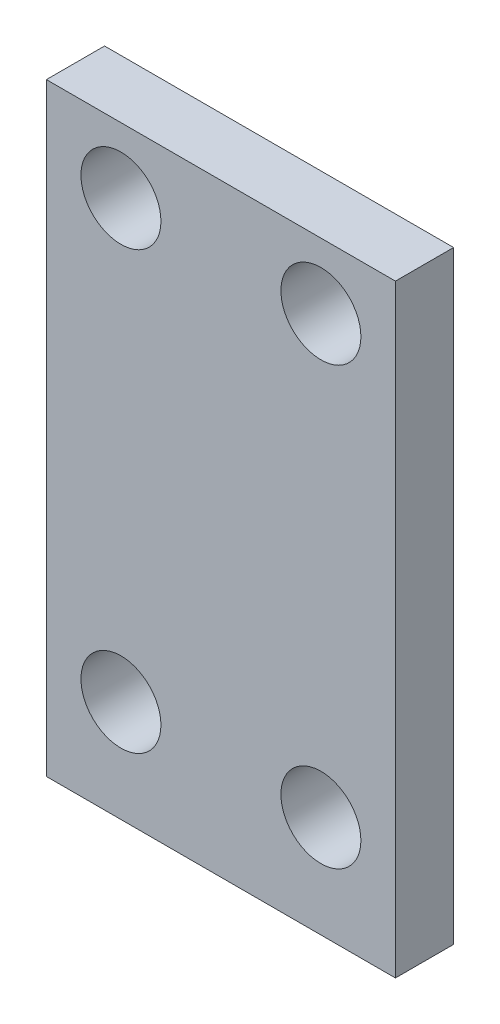
SolidWorks part; units mm, degrees
ref_plane "前视基准面" through (0, 0, 0) normal (0, 0, 1) x (1, 0, 0)
ref_plane "上视基准面" through (0, 0, 0) normal (0, 1, 0) x (1, 0, 0)
ref_plane "右视基准面" through (0, 0, 0) normal (1, 0, 0) x (0, 0, -1)
sketch "草图1" plane through (0, 0, 0) normal (0, 0, 1) x (1, 0, 0)
  circle B0 centre (2.25, 6) radius 1
  line B1 (0, 20) -> (0, 3)
  line B2 (36, 20) -> (0, 20)
  circle B3 centre (7.75, 18) radius 1
  line B4 (10, 3) -> (10, 20)
  line B5 (6, 3) -> (0, 3)
  circle B6 centre (2.25, 18) radius 1
  circle B7 centre (7.75, 6) radius 1
sketch_block_instance "PZM_BASE-1"
sketch_block "PZM_BASE"
sketch "草图2" plane through (0, 0, 0) normal (0, 0, 1) x (1, 0, 0)
  line L0 (0, 20) -> (0, 3) construction
  line L5 (0.2, 3.2) -> (9.8, 3.2)
  line L6 (0.2, 3.2) -> (0.2, 19.8)
  line L7 (0.2, 19.8) -> (9.8, 19.8)
  line L8 (9.8, 3.2) -> (9.8, 19.8)
  line L9 (36, 20) -> (0, 20) construction
  line L10 (10, 3) -> (10, 20) construction
  line L11 (6, 3) -> (0, 3) construction
  circle A0 centre (2.25, 6) radius 1.1
  circle A1 centre (2.25, 18) radius 1.1
  circle A2 centre (7.75, 18) radius 1.1
  circle A3 centre (7.75, 6) radius 1.1
  dimension "D5" = 2.2
  dimension "D1" = 0.2
  dimension "D2" = 0.2
  dimension "D3" = 0.2
  dimension "D4" = 0.2
extrude "凸台-拉伸1" add sketch "草图2" along normal blind 1.6
